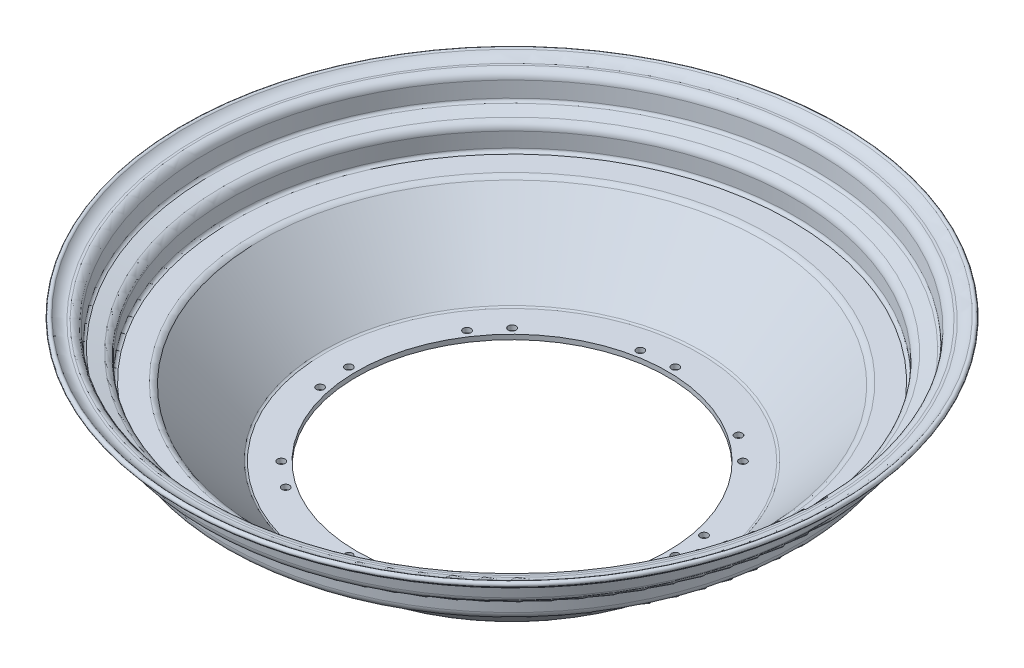
SolidWorks part; units mm, degrees
material "6061-T6 (SS)"
ref_plane "Front Plane" through (0, 0, 0) normal (0, 0, 1) x (1, 0, 0)
ref_plane "Top Plane" through (0, 0, 0) normal (0, 1, 0) x (1, 0, 0)
ref_plane "Right Plane" through (0, 0, 0) normal (1, 0, 0) x (0, 0, -1)
sketch "Sketch3" plane through (0, 0, 0) normal (0, 0, 1) x (1, 0, 0)
  line L0 (-167.2903, 0) -> (0, 0) construction
  line L1 (-102, -45.0065) -> (-122.7594, -45.0065)
  line L2 (-202.8648, 33.0563) -> (-202.016, 23.3542)
  line L3 (-202.8648, 33.0563) -> (-202.8648, 23.7539) construction
  line L4 (-198.0181, 18.7578) -> (-189.6051, 16.8205)
  line L5 (-188.0539, 14.8715) -> (-188.0539, 5.18)
  line L6 (-188.0539, 0) -> (-167.2903, 0) construction
  line L7 (-182.8739, 0) -> (-167.2903, 0)
  line L9 (-199.7019, 33.333) -> (-198.8527, 23.6273)
  line L11 (-197.3091, 21.8526) -> (-188.8965, 19.9154)
  line L12 (-184.8789, 14.8675) -> (-184.8789, 5.175)
  line L13 (-182.8789, 3.175) -> (-168.1576, 3.175)
  line L14 (-184.8789, 18.9902) -> (-184.8789, 3.175) construction
  line L15 (-184.8789, 3.175) -> (-167.2903, 3.175) construction
  line L17 (-201.6878, 19.6028) -> (-188.0539, 16.4633) construction
  line L18 (-188.0539, 16.4633) -> (-188.0539, 0) construction
  line L25 (-204.8572, 38.057) -> (-206.3572, 38.057)
  line L26 (-206.3572, 34.882) -> (-204.8572, 34.882)
  line L34 (-122.708, -41.8885) -> (-102, -41.8885)
  line L35 (-102, -41.8885) -> (-102, -45.0065)
  line L36 (-199.7019, 33.333) -> (-198.726, 22.1789) construction
  line L37 (-198.726, 22.1789) -> (-184.8789, 18.9902) construction
  line L40 (-202.8648, 33.0563) -> (-201.6878, 19.6028) construction
  line L41 (0, 240.889) -> (0, -99.5724) construction
  line L53 (-125, -41.8885) -> (-125, -45.0065) construction
  line L54 (-167.2903, 0) -> (-126.5343, -43.3736)
  line L55 (-164.3826, 1.5421) -> (-124.1655, -41.2581)
  line L59 (-102, -45.0065) -> (-125, -45.0065) construction
  line L60 (-167.2903, 0) -> (-125, -45.0065) construction
  line L61 (-164.9765, 2.1742) -> (-126.2964, -38.9903) construction
  line L62 (-125, -41.8885) -> (-102, -41.8885) construction
  line L63 (-201.8353, 37.083) -> (-201.8353, 37.083) construction
  line L64 (-201.8353, 37.083) -> (-201.8353, 37.083) construction
  line L65 (-126.2964, -38.9903) -> (-126.2964, -38.9903) construction
  line L66 (-126.2964, -38.9903) -> (-126.2964, -38.9903) construction
  line L67 (-126.2964, -38.9903) -> (-126.2964, -38.9903) construction
  arc A2 (-188.0539, 5.18) -> (-182.8739, 0) centre (-182.8739, 5.18) ccw
  arc A6 (-199.7019, 33.333) -> (-204.8572, 38.057) centre (-204.8572, 32.882) ccw
  arc A7 (-199.7019, 33.333) -> (-201.8353, 37.083) centre (-204.8572, 32.882) ccw construction
  arc A8 (-184.8789, 5.175) -> (-182.8789, 3.175) centre (-182.8789, 5.175) ccw
  arc A9 (-189.6051, 16.8205) -> (-188.0539, 14.8715) centre (-190.0539, 14.8715) cw
  arc A10 (-198.8527, 23.6273) -> (-197.3091, 21.8526) centre (-196.8603, 23.8016) ccw
  arc A11 (-188.8965, 19.9154) -> (-184.8789, 14.8675) centre (-190.0589, 14.8675) cw
  arc A12 (-202.016, 23.3542) -> (-198.0181, 18.7578) centre (-196.8557, 23.8057) ccw
  arc A24 (-202.8648, 33.0563) -> (-204.8572, 34.882) centre (-204.8572, 32.882) ccw
  arc A26 (-213.3101, 41.1399) -> (-215.6209, 39.0465) centre (-214.4655, 40.0932) ccw
  arc A27 (-213.3101, 41.1399) -> (-206.3572, 38.057) centre (-206.3572, 47.439) ccw
  arc A28 (-215.6209, 39.0465) -> (-206.3572, 34.882) centre (-206.3058, 47.3819) ccw
  arc A43 (-122.7594, -45.0065) -> (-126.5343, -43.3736) centre (-122.7594, -39.8265) cw
  arc A44 (-164.3826, 1.5421) -> (-168.1576, 3.175) centre (-168.1576, -2.005) ccw
  arc A45 (-122.708, -41.8885) -> (-124.1655, -41.2581) centre (-122.708, -39.8885) cw
  arc A46 (-201.8353, 37.083) -> (-201.8353, 37.083) centre (-201.8353, 37.083) cw construction
  arc A47 (-201.8353, 37.083) -> (-201.8353, 37.083) centre (-201.8353, 37.083) ccw construction
  arc A48 (-201.8353, 37.083) -> (-201.8353, 37.083) centre (-201.8353, 37.083) ccw construction
  point P7 (-102, -43.4475)
  dimension "D5" = 2
  dimension "D6" = 2
  dimension "D4" = 5.175
  dimension "D7" = 5.18
  dimension "D11" = 5.18
  dimension "D12" = 2
  dimension "D9" = 5.18
  dimension "D2" = 5
  dimension "D3" = 3.175
  dimension "D8" = 102
  dimension "D10" = 3.175
revolve "Revolve2" add sketch "Sketch3" angle 360 about L41
sketch "Sketch4" plane through (0, 0, 0) normal (0, 1, 0) x (1, 0, 0)
  line L0 (0, 0) -> (0, 107) construction
  line L1 (0, 0) -> (-20.8747, 104.944) construction
  circle A0 centre (0, 107) radius 2.5
  circle A1 centre (-3884.1816, -9484.2438) radius 2.5
  circle A2 centre (-13412.7463, -13519.7463) radius 2.5
  circle A3 centre (-23003.9901, -9635.5647) radius 2.5
  circle A4 centre (-27039.4925, -107) radius 2.5
  circle A5 centre (-23155.3109, 9484.2438) radius 2.5
  circle A6 centre (-13626.7463, 13519.7463) radius 2.5
  circle A7 centre (-4035.5024, 9635.5647) radius 2.5
  circle A8 centre (-20.8747, 104.944) radius 2.5
  circle A9 centre (-3900.396, -9470.937) radius 2.5
  circle A10 centre (-13414.8022, -13498.8716) radius 2.5
  circle A11 centre (-22990.6833, -9619.3503) radius 2.5
  circle A12 centre (-27018.6178, -104.944) radius 2.5
  circle A13 centre (-23139.0965, 9470.937) radius 2.5
  circle A14 centre (-13624.6903, 13498.8716) radius 2.5
  circle A15 centre (-4048.8092, 9619.3503) radius 2.5
  circle A16 centre (75.6604, 75.6604) radius 2.5
  circle A17 centre (59.446, 88.9672) radius 2.5
  circle A18 centre (107, 0) radius 2.5
  circle A19 centre (104.944, 20.8747) radius 2.5
  circle A20 centre (75.6604, -75.6604) radius 2.5
  circle A21 centre (88.9672, -59.446) radius 2.5
  circle A22 centre (0, -107) radius 2.5
  circle A23 centre (20.8747, -104.944) radius 2.5
  circle A24 centre (-75.6604, -75.6604) radius 2.5
  circle A25 centre (-59.446, -88.9672) radius 2.5
  circle A26 centre (-107, 0) radius 2.5
  circle A27 centre (-104.944, -20.8747) radius 2.5
  circle A28 centre (-75.6604, 75.6604) radius 2.5
  circle A29 centre (-88.9672, 59.446) radius 2.5
  point P19 (-13519.7463, 0)
  point P37 (-13519.7463, 0)
  point P67 (0, 0)
  dimension "D1" = 107
  dimension "D2" = 5
  dimension "D4" = 11.25
  dimension "D5" = 8
  dimension "D3" = 8
  dimension "D6" = 8
extrude "Cut-Extrude3" cut sketch "Sketch4" against normal through all both and the other way through all
